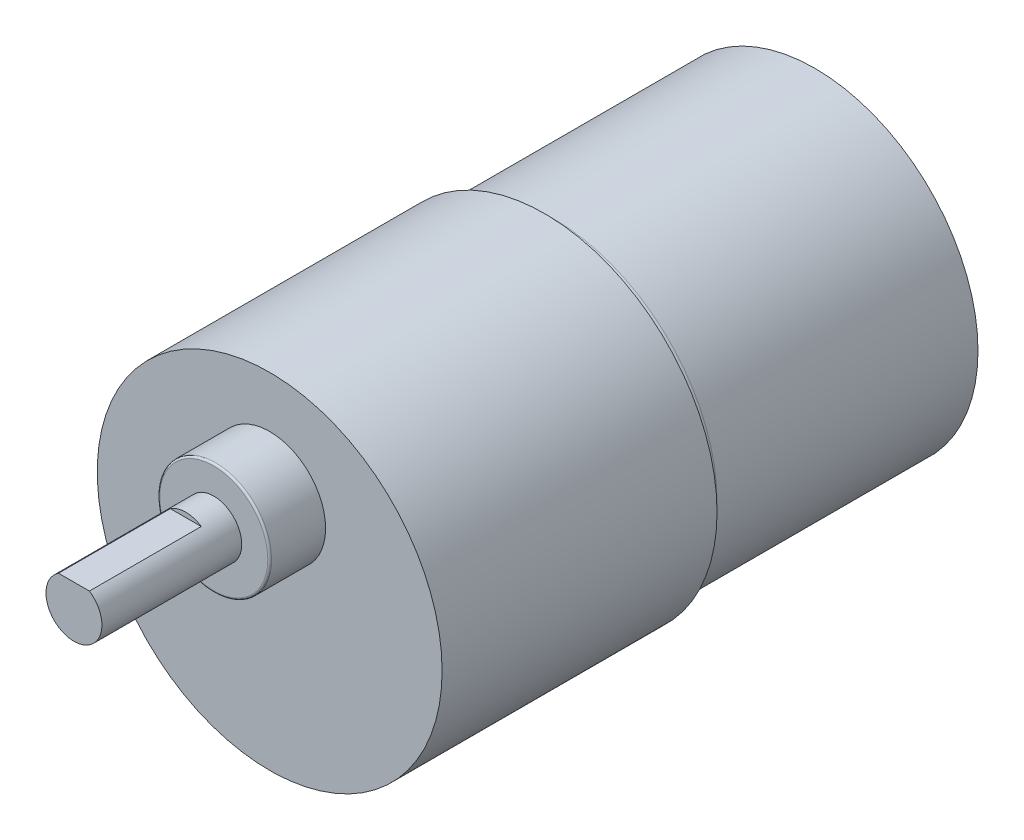
SolidWorks part; units mm, degrees
ref_plane "Front Plane" through (0, 0, 0) normal (0, 0, 1) x (1, 0, 0)
ref_plane "Top Plane" through (0, 0, 0) normal (0, 1, 0) x (1, 0, 0)
ref_plane "Right Plane" through (0, 0, 0) normal (1, 0, 0) x (0, 0, -1)
sketch "Sketch2" plane through (0, 0, 0) normal (0, 0, 1) x (1, 0, 0)
  circle A0 centre (0, 0) radius 17.5
extrude "Boss-Extrude2" add sketch "Sketch2" along normal blind 29
fillet "Fillet2" radius 1 1 edges at (17.5, 0, 29)
sketch "Sketch3" plane through (0, 0, 29) normal (0, 0, 1) x (1, 0, 0)
  circle A0 centre (0, 0) radius 18.5
extrude "Boss-Extrude3" add sketch "Sketch3" along normal blind 29.5
sketch "Sketch4" plane through (0, 0, 58.5) normal (0, 0, 1) x (1, 0, 0)
  line L0 (0, 0) -> (0, 7)
  circle A0 centre (0, 7) radius 6
extrude "Boss-Extrude4" add sketch "Sketch4" along normal blind 6
fillet "Fillet6" radius 0.2 1 edges at (6, 7, 64.5)
sketch "Sketch5" plane through (0, 0, 64.5) normal (0, 0, 1) x (1, 0, 0)
  circle A0 centre (0, 7) radius 3
extrude "Boss-Extrude5" add sketch "Sketch5" along normal blind 3
sketch "Sketch6" plane through (0, 0, 67.5) normal (0, 0, 1) x (1, 0, 0)
  line L0 (0, 7) -> (0, 9.5)
  line L2 (-1.6583, 9.5) -> (1.6583, 9.5)
  arc A0 (1.6583, 9.5) -> (-1.6583, 9.5) centre (0, 7) cw
  circle A1 centre (0, 7) radius 3 construction
  point P9 (0, 0)
  point P10 (0, 0)
  point P11 (-1.6575, 9.5006)
extrude "Boss-Extrude6" add sketch "Sketch6" along normal blind 12 contours L2 A0
